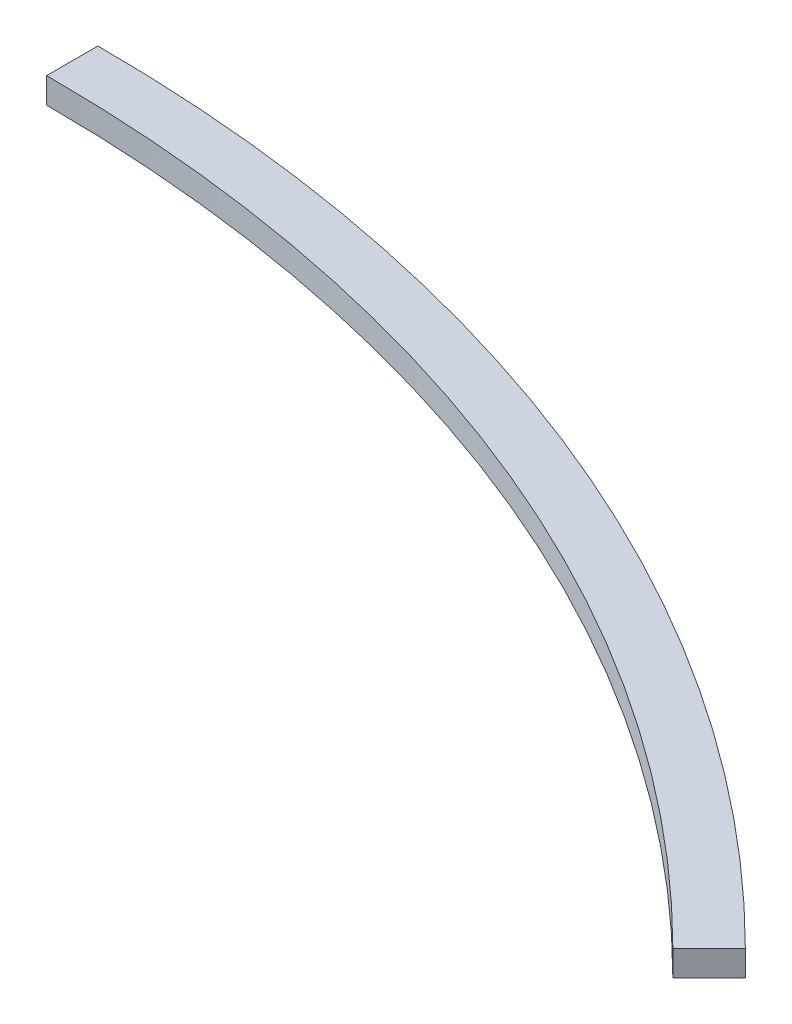
SolidWorks part; units mm, degrees
ref_plane "Front Plane" through (0, 0, 0) normal (0, 0, 1) x (1, 0, 0)
ref_plane "Top Plane" through (0, 0, 0) normal (0, 1, 0) x (1, 0, 0)
ref_plane "Right Plane" through (0, 0, 0) normal (1, 0, 0) x (0, 0, -1)
sketch "Sketch1" plane through (0, 0, 0) normal (0, 1, 0) x (1, 0, 0)
  line L0 (0, 0) -> (0, 590) construction
  line L1 (0, 0) -> (431.3351, 431.3351) construction
  line L2 (0, 590) -> (0, 610)
  line L3 (417.193, 417.193) -> (431.3351, 431.3351)
  arc A0 (0, 590) -> (417.193, 417.193) centre (0, 0) cw
  arc A1 (0, 610) -> (431.3351, 431.3351) centre (0, 0) cw
  dimension "D1" = 20
  dimension "D2" = 610
  dimension "D3" = 590
  dimension "D4" = 45
extrude "Boss-Extrude1" add sketch "Sketch1" along normal blind 10 contours A1 L2 A0 L3
